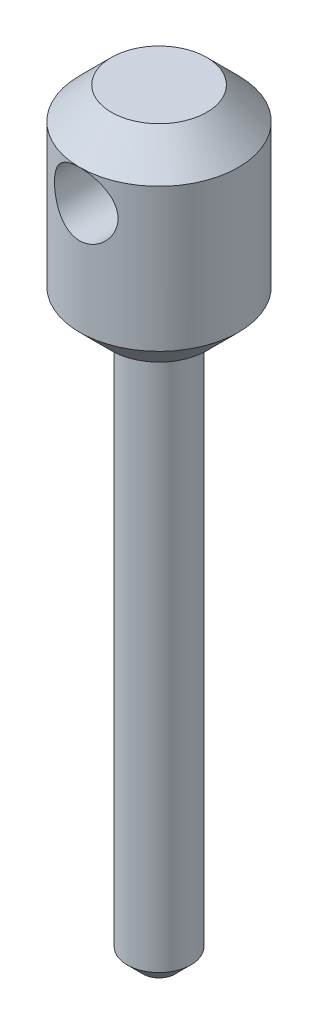
SolidWorks part; units mm, degrees
ref_plane "Front Plane" through (0, 0, 0) normal (0, 0, 1) x (1, 0, 0)
ref_plane "Top Plane" through (0, 0, 0) normal (0, 1, 0) x (1, 0, 0)
ref_plane "Right Plane" through (0, 0, 0) normal (1, 0, 0) x (0, 0, -1)
sketch "Sketch1" plane through (0, 0, 0) normal (0, 0, 1) x (1, 0, 0)
  line L0 (0, 0) -> (0, 55.0144) construction
  line L1 (0, 0) -> (1, 0)
  line L2 (2, 1) -> (2, 35)
  line L3 (2, 35) -> (3, 35)
  line L5 (5, 37) -> (5, 46)
  line L6 (3, 48) -> (0, 48)
  line L8 (3, 35) -> (5, 37)
  line L9 (0, 0) -> (0, 48)
  line L10 (1, 0) -> (2, 1)
  line L11 (5, 46) -> (3, 48)
  point P3 (5, 45.0507)
  point P4 (2, 0)
  point P6 (5, 48)
  point P7 (5, 45.1425)
  point P8 (5, 35)
  point P9 (0, 0)
  point P10 (5, 48)
  point P11 (5, 48)
  point P12 (5, 48)
  point P14 (5, 35)
  point P15 (5, 35.1341)
  point P16 (4.8588, 48)
  point P20 (0, 0)
  point P23 (5, 47.8842)
  dimension "D3" = 5
  dimension "D5" = 45
  dimension "D1" = 2
  dimension "D2" = 35
  dimension "D4" = 2
  dimension "D6" = 13
  dimension "D7" = 2
  dimension "D9" = 45
  dimension "D12" = 1
  dimension "D13" = 45
revolve "Revolve1" add sketch "Sketch1" angle 360 about L0
sketch "Sketch2" plane through (0, 0, 0) normal (0, 0, 1) x (1, 0, 0)
  line L0 (-3, 35) -> (3, 35) construction
  circle A0 centre (0, 44) radius 2
  point P2 (0, 0)
  dimension "D1" = 4
  dimension "D2" = 9
extrude "Cut-Extrude1" cut sketch "Sketch2" against normal through all both and the other way through all
